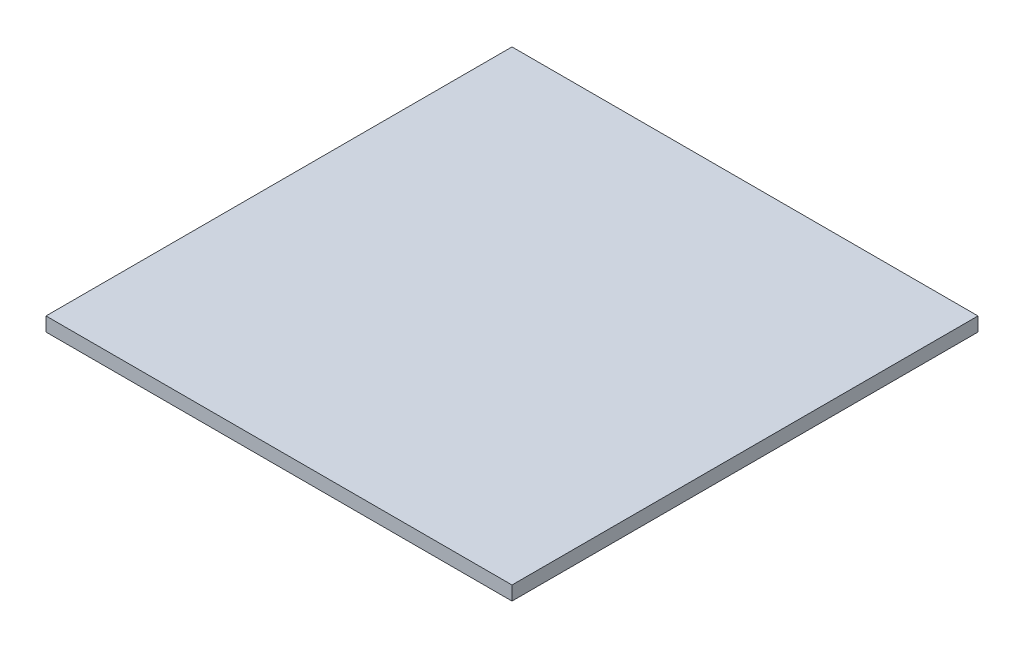
SolidWorks part; units mm, degrees
ref_plane "Plan de face" through (0, 0, 0) normal (0, 0, 1) x (1, 0, 0)
ref_plane "Plan de dessus" through (0, 0, 0) normal (0, 1, 0) x (1, 0, 0)
ref_plane "Plan de droite" through (0, 0, 0) normal (1, 0, 0) x (0, 0, -1)
sketch "Esquisse1" plane through (0, 0, 0) normal (0, 1, 0) x (1, 0, 0)
  line L1 (0, 0) -> (100, 0)
  line L2 (0, 0) -> (0, 100)
  line L3 (0, 100) -> (100, 100)
  line L4 (100, 0) -> (100, 100)
  dimension "D1" = 100
  dimension "D2" = 100
extrude "Boss.-Extru.1" add sketch "Esquisse1" along normal blind 3
